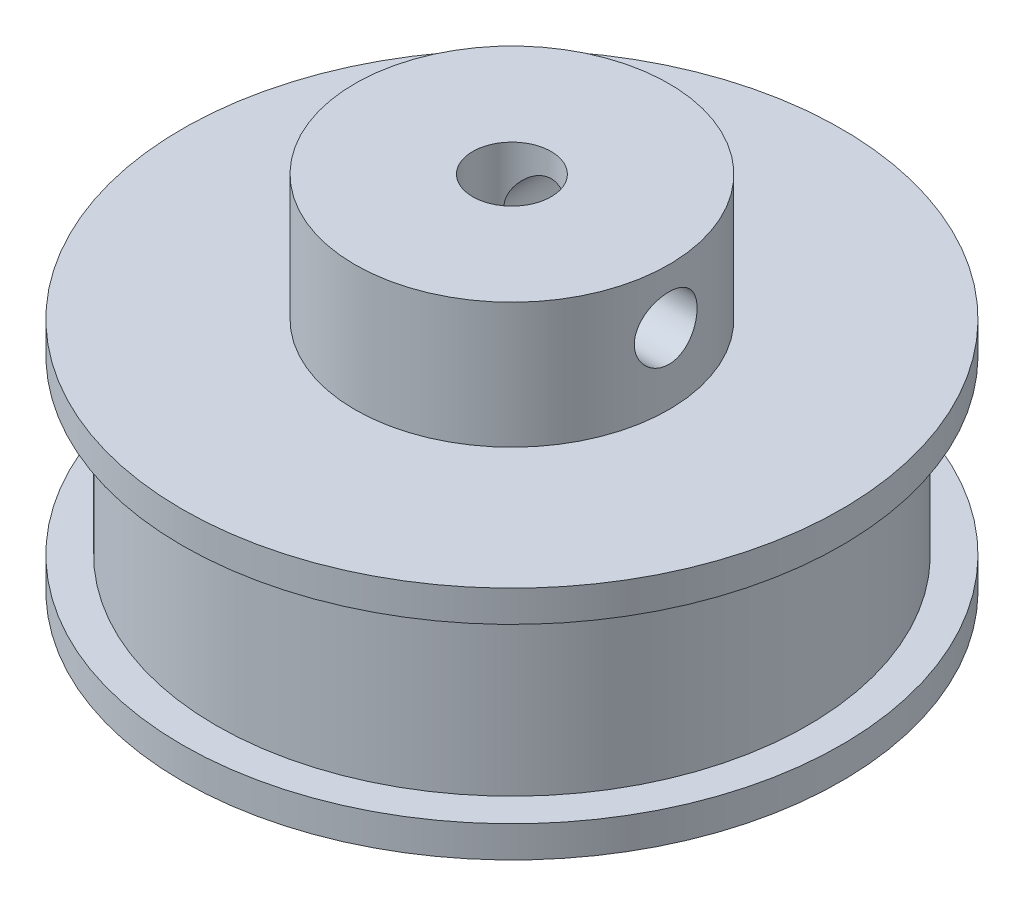
SolidWorks part; units mm, degrees
ref_plane "Front Plane" through (0, 0, 0) normal (0, 0, 1) x (1, 0, 0)
ref_plane "Top Plane" through (0, 0, 0) normal (0, 1, 0) x (1, 0, 0)
ref_plane "Right Plane" through (0, 0, 0) normal (1, 0, 0) x (0, 0, -1)
sketch "Sketch1" plane through (0, 0, 0) normal (0, 1, 0) x (1, 0, 0)
  circle A0 centre (0, 0) radius 21
  dimension "D1" = 42
extrude "Boss-Extrude1" add sketch "Sketch1" along normal blind 2
sketch "Sketch2" plane through (0, 2, 0) normal (0, 1, 0) x (1, 0, 0)
  circle A0 centre (0, 0) radius 18.85
  dimension "D1" = 37.7
extrude "Boss-Extrude2" add sketch "Sketch2" along normal blind 11
sketch "Sketch3" plane through (0, 13, 0) normal (0, 1, 0) x (1, 0, 0)
  circle A0 centre (0, 0) radius 21
  circle A1 centre (0, 0) radius 21 construction
extrude "Boss-Extrude3" add sketch "Sketch3" along normal blind 2
sketch "Sketch4" plane through (0, 15, 0) normal (0, 1, 0) x (1, 0, 0)
  circle A0 centre (0, 0) radius 10
  dimension "D1" = 20
extrude "Boss-Extrude4" add sketch "Sketch4" along normal blind 8
sketch "Sketch5" plane through (0, 23, 0) normal (0, 1, 0) x (1, 0, 0)
  circle A0 centre (0, 0) radius 2.5
  dimension "D1" = 5
extrude "Cut-Extrude1" cut sketch "Sketch5" against normal through all
sketch "Sketch6" plane through (0, 0, 0) normal (0, 0, 1) x (1, 0, 0)
  line L0 (10, 23) -> (-10, 23) construction
  circle A0 centre (0, 19.5) radius 2
  dimension "D1" = 4
  dimension "D2" = 3.5
extrude "Cut-Extrude2" cut sketch "Sketch6" against normal through all
pattern_circular "CirPattern1" count 2 every 90 about axis through (0, 23, 0) along (0, -1, 0) of "Cut-Extrude2"
